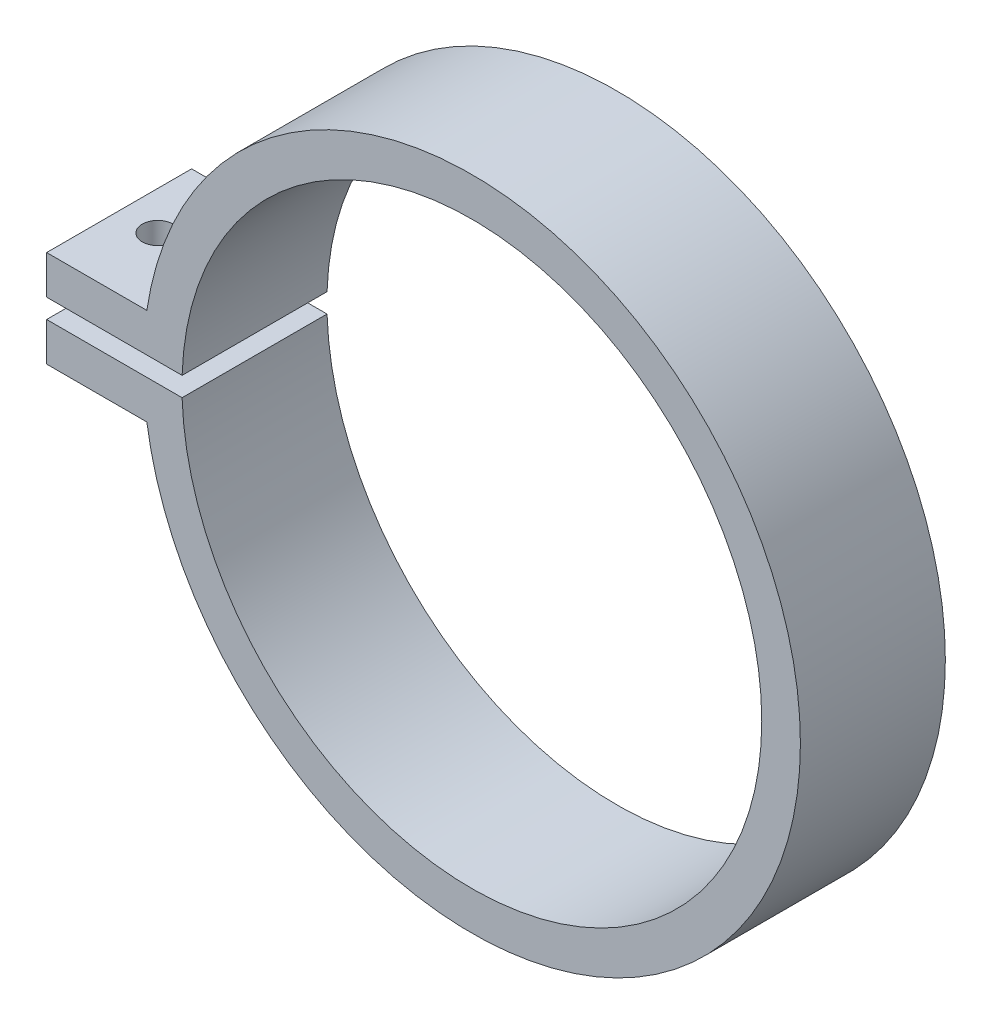
SolidWorks part; units mm, degrees
ref_plane "Front Plane" through (0, 0, 0) normal (0, 0, 1) x (1, 0, 0)
ref_plane "Top Plane" through (0, 0, 0) normal (0, 1, 0) x (1, 0, 0)
ref_plane "Right Plane" through (0, 0, 0) normal (1, 0, 0) x (0, 0, -1)
sketch "Sketch1" plane through (0, 0, 0) normal (0, 0, 1) x (1, 0, 0)
  line L0 (0, 0) -> (0, -50000) construction
  circle A1 centre (0, 0) radius 34
  dimension "D2" = 68
extrude "Boss-Extrude1" add sketch "Sketch1" along normal mid plane 15 contours A1
sketch "Sketch4" plane through (0, 0, 0) normal (0, 0, 1) x (1, 0, 0)
  line L1 (-44, 5) -> (0, 5)
  line L2 (-44, 5) -> (-44, -5)
  line L3 (-44, -5) -> (0, -5)
  line L4 (0, 5) -> (0, -5)
  line L5 (-44, 5) -> (0, -5) construction
  line L6 (-44, -5) -> (0, 5) construction
  point P0 (-22, 0)
  dimension "D1" = 44
  dimension "D2" = 10
extrude "Boss-Extrude2" add sketch "Sketch4" along normal mid plane 15
sketch "Sketch5" plane through (0, 0, 7.5) normal (0, 0, 1) x (1, 0, 0)
  line L0 (-44, 5) -> (-44, -5) construction
  line L1 (-44, 1) -> (0, 1)
  line L2 (-44, 1) -> (-44, -1)
  line L3 (-44, -1) -> (0, -1)
  line L4 (0, 1) -> (0, -1)
  line L5 (-44, 1) -> (0, -1) construction
  line L6 (-44, -1) -> (0, 1) construction
  circle A0 centre (0, 0) radius 30
  point P6 (-22, 0)
  dimension "D1" = 60
  dimension "D2" = 2
extrude "Cut-Extrude1" cut sketch "Sketch5" against normal blind 26.5 contours A0 | L3 L4 L1 L2
sketch "Sketch6" plane through (0, 5, 0) normal (0, 1, 0) x (1, 0, 0)
  line L0 (-44, -7.5) -> (-44, 7.5) construction
  circle A0 centre (-40, 0) radius 1.6
  dimension "D1" = 3.2
  dimension "D2" = 4
extrude "Cut-Extrude2" cut sketch "Sketch6" against normal up to surface (10 mm away) and the other way through all up to face at (-38.8152, -5, 0)
